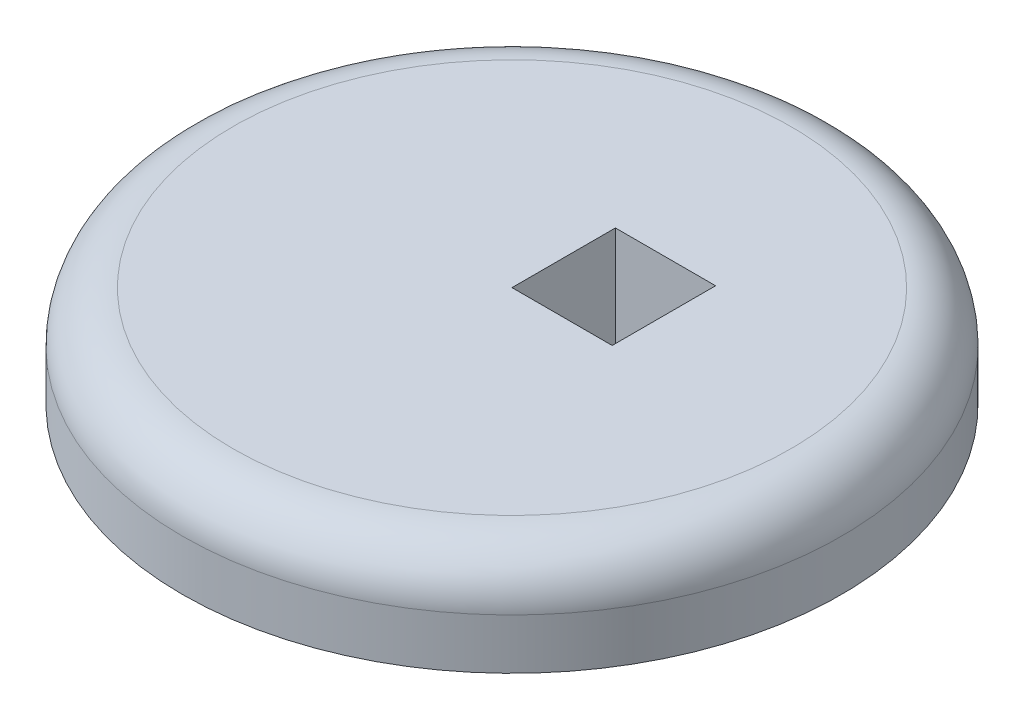
SolidWorks part; units mm, degrees
ref_plane "Front Plane" through (0, 0, 0) normal (0, 0, 1) x (1, 0, 0)
ref_plane "Top Plane" through (0, 0, 0) normal (0, 1, 0) x (1, 0, 0)
ref_plane "Right Plane" through (0, 0, 0) normal (1, 0, 0) x (0, 0, -1)
sketch "Sketch1" plane through (0, 0, 0) normal (0, 1, 0) x (1, 0, 0)
  circle A0 centre (0, 0) radius 32.6251
extrude "Boss-Extrude1" add sketch "Sketch1" along normal blind 10
fillet "Fillet1" radius 5 1 edges at (0, 10, 32.6251)
sketch "Sketch2" plane through (0, 10, 0) normal (0, 1, 0) x (1, 0, 0)
  line L1 (0, 0) -> (9.9185, 0)
  line L2 (0, 0) -> (0, 10.237)
  line L3 (0, 10.237) -> (9.9185, 10.237)
  line L4 (9.9185, 0) -> (9.9185, 10.237)
extrude "Cut-Extrude1" cut sketch "Sketch2" against normal blind 10
